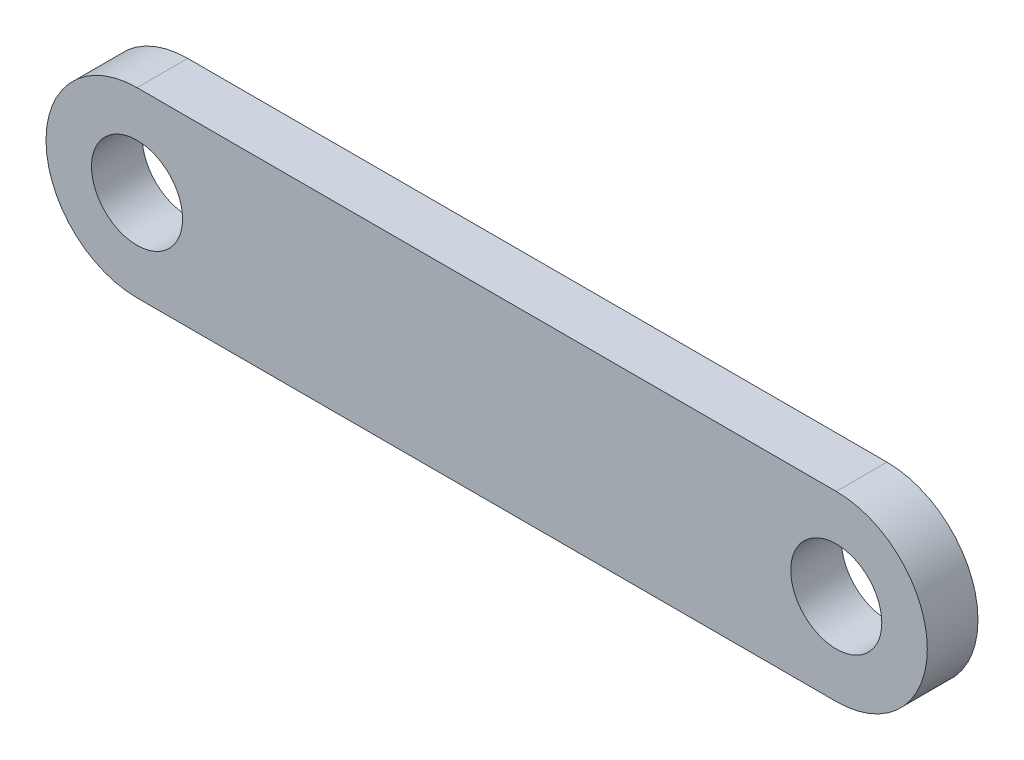
SolidWorks part; units mm, degrees
ref_plane "Front Plane" through (0, 0, 0) normal (0, 0, 1) x (1, 0, 0)
ref_plane "Top Plane" through (0, 0, 0) normal (0, 1, 0) x (1, 0, 0)
ref_plane "Right Plane" through (0, 0, 0) normal (1, 0, 0) x (0, 0, -1)
sketch "Sketch1" plane through (0, 0, 0) normal (0, 0, 1) x (1, 0, 0)
  line L0 (-34.49, 0) -> (34.49, 0)
  line L1 (-34.49, 8.98) -> (34.49, 8.98)
  line L2 (-34.49, -8.98) -> (34.49, -8.98)
  circle A0 centre (-34.49, 0) radius 4.49
  circle A1 centre (34.49, 0) radius 4.49
  circle A2 centre (-34.49, 0) radius 8.98
  circle A3 centre (34.49, 0) radius 8.98
  point P4 (0, 0)
extrude "Boss-Extrude1" add sketch "Sketch1" along normal blind 5
